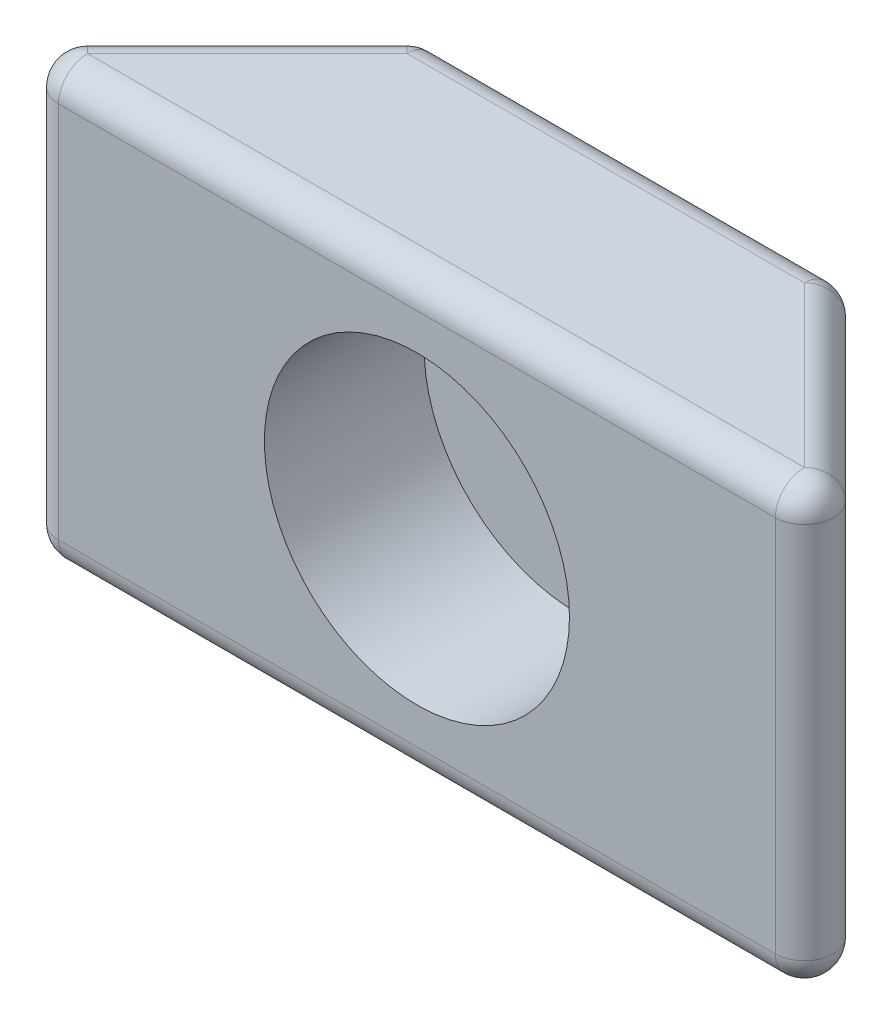
SolidWorks part; units mm, degrees
ref_plane "前视基准面" through (0, 0, 0) normal (0, 0, 1) x (1, 0, 0)
ref_plane "上视基准面" through (0, 0, 0) normal (0, 1, 0) x (1, 0, 0)
ref_plane "右视基准面" through (0, 0, 0) normal (1, 0, 0) x (0, 0, -1)
other "Configuration Table"
sketch "草图2" plane through (0, 0, 0) normal (0, 1, 0) x (1, 0, 0)
  line L0 (-5.9, 0) -> (5.9, 0)
  line L1 (5.9, 0) -> (2.9, 3)
  line L2 (2.9, 3) -> (-2.9, 3)
  line L3 (-2.9, 3) -> (-5.9, 0)
  point P2 (0, 0)
  dimension "D1" = 5.8
  dimension "D2" = 3
  dimension "D3" = 45
  dimension "D4" = 45
extrude "凸台-拉伸1" add sketch "草图2" along normal mid plane 6
sketch "草图3" plane through (0, 0, 0) normal (0, 0, 1) x (1, 0, 0)
  circle A0 centre (0, 0) radius 2.1
  dimension "D1" = 4.2
extrude "切除-拉伸1" cut sketch "草图3" against normal blind 2.2
fillet "圆角1" radius 0.4 12 edges at (0, 3, -3) (0, 3, 0) (0, -3, 0) (0, -3, -3) (5.9, 0, 0) (4.4, 3, -1.5) (2.9, 0, -3) (4.4, -3, -1.5) (-2.9, 0, -3) (-4.4, 3, -1.5) (-5.9, 0, 0) (-4.4, -3, -1.5)
